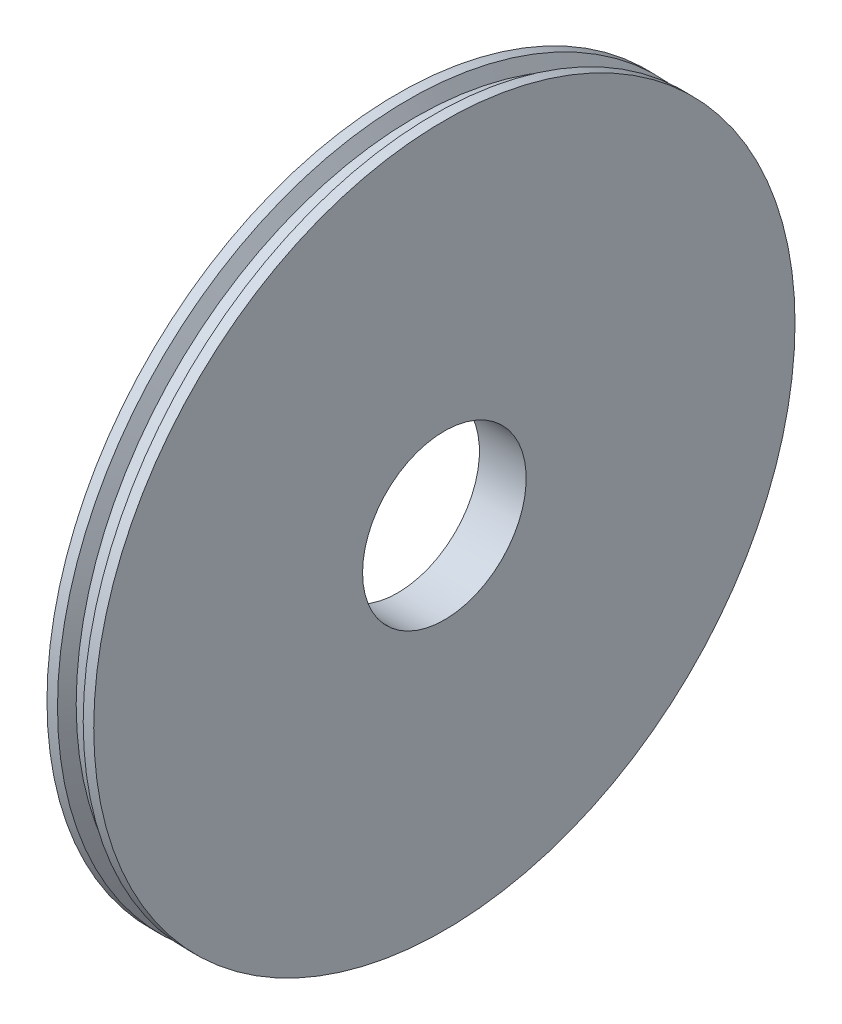
SolidWorks part; units mm, degrees
material "Slitinová ocel"
ref_plane "Přední rovina" through (0, 0, 0) normal (0, 0, 1) x (1, 0, 0)
ref_plane "Horní rovina" through (0, 0, 0) normal (0, 1, 0) x (1, 0, 0)
ref_plane "Pravá rovina" through (0, 0, 0) normal (1, 0, 0) x (0, 0, -1)
sketch "Skica1" plane through (0, 0, 0) normal (0, 0, 1) x (1, 0, 0)
  line L0 (-10, 35) -> (-10, 150)
  line L1 (-10, 150) -> (-5.5, 150)
  line L2 (-5.5, 150) -> (-2.5, 145)
  line L3 (-2.5, 145) -> (2.5, 145)
  line L4 (2.5, 145) -> (5.5, 150)
  line L5 (5.5, 150) -> (10, 150)
  line L6 (10, 35) -> (10, 150)
  line L7 (10, 35) -> (-10, 35)
  line L8 (-72.5197, 0) -> (82.6634, 0) construction
  point P3 (0, 35)
  dimension "D1" = 20
  dimension "D2" = 115
  dimension "D3" = 4.5
  dimension "D4" = 5
  dimension "D5" = 4.5
  dimension "D6" = 3
  dimension "D7" = 3
  dimension "D8" = 5
  dimension "D9" = 5
  dimension "D10" = 35
revolve "Rotovat1" add sketch "Skica1" angle 360 about L8
